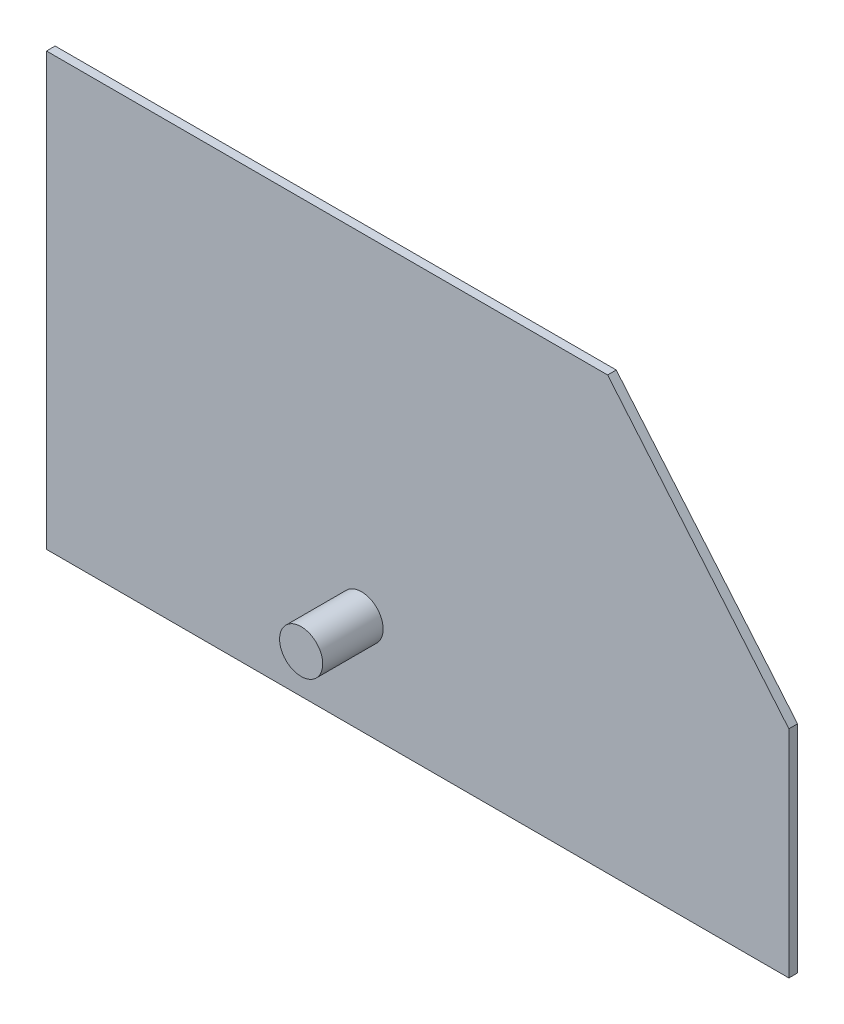
SolidWorks part; units mm, degrees
material "1023 Carbon Steel Sheet (SS)"
ref_plane "Front Plane" through (0, 0, 0) normal (0, 0, 1) x (1, 0, 0)
ref_plane "Top Plane" through (0, 0, 0) normal (0, 1, 0) x (1, 0, 0)
ref_plane "Right Plane" through (0, 0, 0) normal (1, 0, 0) x (0, 0, -1)
sketch "Sketch1" plane through (0, 0, 0) normal (0, 0, 1) x (1, 0, 0)
  line L0 (0, 0) -> (86, 0)
  line L1 (86, 0) -> (86, 25)
  line L2 (86, 25) -> (65, 50)
  line L3 (65, 50) -> (0, 50)
  line L4 (0, 50) -> (0, 0)
  dimension "D1" = 86
  dimension "D2" = 25
  dimension "D3" = 50
  dimension "D4" = 65
extrude "Boss-Extrude1" add sketch "Sketch1" along normal blind 1
sketch "Sketch3" plane through (0, 0, 1) normal (0, 0, 1) x (1, 0, 0)
  line L0 (86, 0) -> (86, 25) construction
  line L1 (0, 0) -> (86, 0) construction
  circle A0 centre (36.5, 11.5) radius 2.5
  dimension "D1" = 5
  dimension "D2" = 49.5
  dimension "D3" = 11.5
extrude "Boss-Extrude3" add sketch "Sketch3" along normal blind 7
